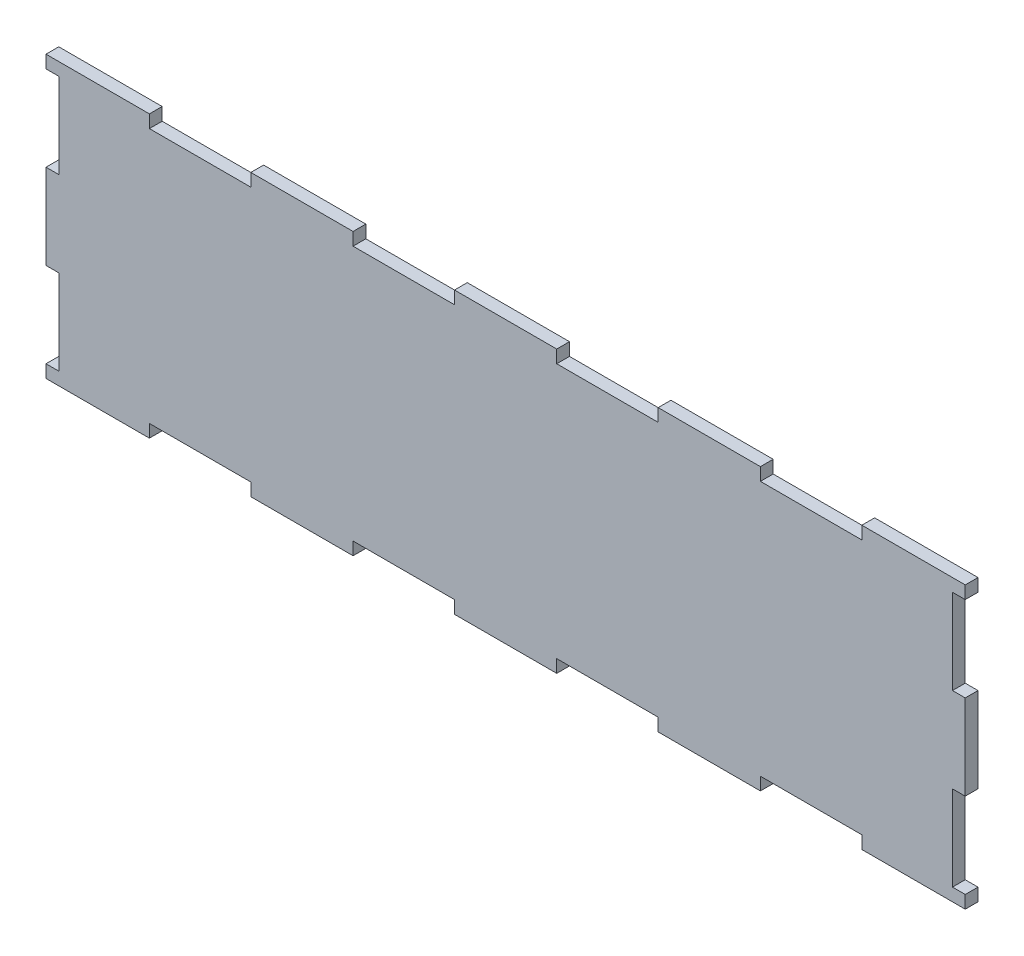
SolidWorks part; units mm, degrees
ref_plane "Front Plane" through (0, 0, 0) normal (0, 0, 1) x (1, 0, 0)
ref_plane "Top Plane" through (0, 0, 0) normal (0, 1, 0) x (1, 0, 0)
ref_plane "Right Plane" through (0, 0, 0) normal (1, 0, 0) x (0, 0, -1)
sketch "Sketch1" plane through (0, 0, 0) normal (0, 0, 1) x (1, 0, 0)
  line L0 (-83.6941, 3) -> (-107.9892, 3)
  line L1 (-107.9892, 3) -> (-107.9892, 6)
  line L2 (-107.9892, 6) -> (-104.9892, 6)
  line L3 (-104.9892, 6) -> (-104.9892, 26)
  line L4 (-104.9892, 26) -> (-107.9892, 26)
  line L5 (-107.9892, 26) -> (-107.9892, 46)
  line L6 (-107.9892, 46) -> (-104.9892, 46)
  line L7 (-104.9892, 46) -> (-104.9892, 66)
  line L8 (-104.9892, 66) -> (-107.9892, 66)
  line L9 (-107.9892, 66) -> (-107.9892, 69)
  line L10 (-107.9892, 69) -> (-83.6941, 69)
  line L11 (-83.6941, 69) -> (-83.6941, 66)
  line L12 (-83.6941, 66) -> (-59.8579, 66)
  line L13 (-59.8579, 66) -> (-59.8579, 69)
  line L14 (-59.8579, 69) -> (-35.8362, 69)
  line L15 (-35.8362, 69) -> (-35.8362, 66)
  line L16 (-35.8362, 66) -> (-12, 66)
  line L17 (-12, 66) -> (-12, 69)
  line L18 (-12, 69) -> (12.0217, 69)
  line L19 (12.0217, 69) -> (12.0217, 66)
  line L20 (12.0217, 66) -> (35.8579, 66)
  line L21 (35.8579, 66) -> (35.8579, 69)
  line L22 (35.8579, 69) -> (59.8796, 69)
  line L23 (59.8796, 69) -> (59.8796, 66)
  line L24 (59.8796, 66) -> (83.7158, 66)
  line L25 (83.7158, 66) -> (83.7158, 69)
  line L26 (83.7158, 69) -> (108.0108, 69)
  line L27 (108.0108, 69) -> (108.0108, 66)
  line L28 (108.0108, 66) -> (105.0108, 66)
  line L29 (105.0108, 66) -> (105.0108, 46)
  line L30 (105.0108, 46) -> (108.0108, 46)
  line L31 (108.0108, 46) -> (108.0108, 26)
  line L32 (108.0108, 26) -> (105.0108, 26)
  line L33 (105.0108, 26) -> (105.0108, 6)
  line L34 (105.0108, 6) -> (108.0108, 6)
  line L35 (108.0108, 6) -> (108.0108, 3)
  line L36 (108.0108, 3) -> (83.7158, 3)
  line L37 (83.7158, 3) -> (83.7158, 6)
  line L38 (59.8796, 6) -> (59.8796, 3)
  line L39 (59.8796, 3) -> (35.8579, 3)
  line L40 (35.8579, 3) -> (35.8579, 6)
  line L41 (35.8579, 6) -> (12.0217, 6)
  line L42 (12.0217, 6) -> (12.0217, 3)
  line L43 (12.0217, 3) -> (-12, 3)
  line L44 (-12, 3) -> (-12, 6)
  line L45 (-35.8362, 6) -> (-35.8362, 3)
  line L46 (-35.8362, 3) -> (-59.8579, 3)
  line L47 (-59.8579, 3) -> (-59.8579, 6)
  line L48 (-59.8579, 6) -> (-83.6941, 6)
  line L49 (-83.6941, 6) -> (-83.6941, 3)
  line L50 (-35.8362, 6) -> (-12, 6)
  line L51 (83.7158, 6) -> (59.8796, 6)
  dimension "D1" = 60
  dimension "D2" = 210
  dimension "D3" = 3
  dimension "D4" = 3
extrude "Boss-Extrude1" add sketch "Sketch1" along normal blind 3
